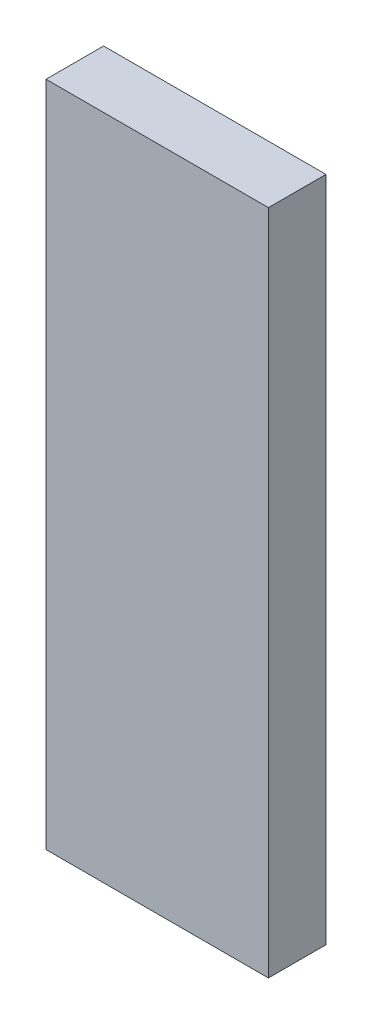
SolidWorks part; units mm, degrees
material "Polyurethane Foam Flexible"
ref_plane "Front Plane" through (0, 0, 0) normal (0, 0, 1) x (1, 0, 0)
ref_plane "Top Plane" through (0, 0, 0) normal (0, 1, 0) x (1, 0, 0)
ref_plane "Right Plane" through (0, 0, 0) normal (1, 0, 0) x (0, 0, -1)
sketch "Sketch1" plane through (0, 0, 0) normal (0, 0, 1) x (1, 0, 0)
  line L0 (35.165, 24.84) -> (35.165, -24.84) construction
  line L1 (16.115, 19.05) -> (28.815, 19.05)
  line L2 (16.115, 19.05) -> (16.115, -19.05)
  line L3 (16.115, -19.05) -> (28.815, -19.05)
  line L4 (28.815, 19.05) -> (28.815, -19.05)
  line L5 (16.115, 19.05) -> (28.815, -19.05) construction
  line L6 (16.115, -19.05) -> (28.815, 19.05) construction
  line L7 (0, 0) -> (0, 24.84) construction
  line L8 (-35.165, 24.84) -> (35.165, 24.84) construction
  line L9 (-16.115, -19.05) -> (-28.815, 19.05) construction
  line L10 (-16.115, 19.05) -> (-28.815, -19.05) construction
  line L11 (-28.815, 19.05) -> (-28.815, -19.05)
  line L12 (-16.115, -19.05) -> (-28.815, -19.05)
  line L13 (-16.115, 19.05) -> (-16.115, -19.05)
  line L14 (-16.115, 19.05) -> (-28.815, 19.05)
  point P4 (22.465, 0)
  point P17 (-22.465, 0)
  dimension "D1" = 12.7
  dimension "D2" = 38.1
  dimension "D3" = 6.35
extrude "Boss-Extrude1" add sketch "Sketch1" along normal blind 3.2868
delete or keep bodies "Body-Delete/Keep 1" type delete bodies bodies 101
